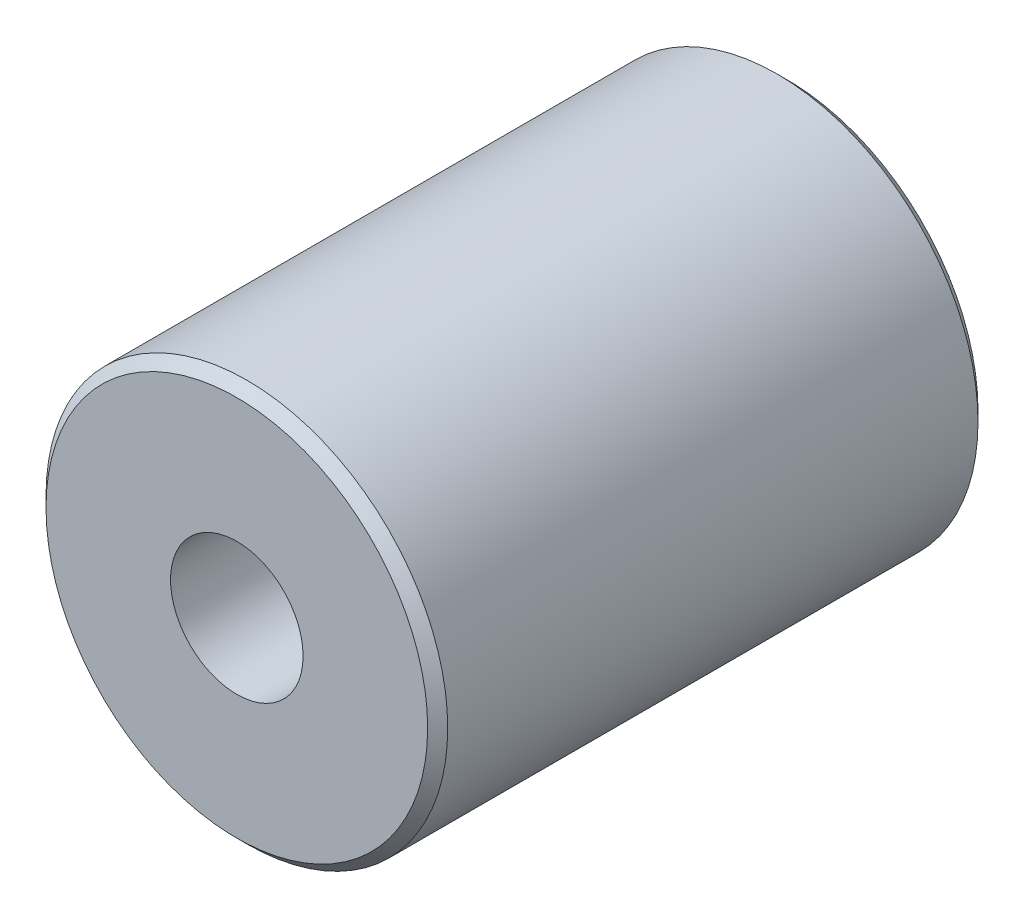
SolidWorks part; units mm, degrees
ref_plane "Front Plane" through (0, 0, 0) normal (0, 0, 1) x (1, 0, 0)
ref_plane "Top Plane" through (0, 0, 0) normal (0, 1, 0) x (1, 0, 0)
ref_plane "Right Plane" through (0, 0, 0) normal (1, 0, 0) x (0, 0, -1)
sketch "Sketch1" plane through (0, 0, 0) normal (0, 0, 1) x (1, 0, 0)
  circle A1 centre (0, 0) radius 5
extrude "Extrude1" add sketch "Sketch1" against normal blind 13.7
hole_wizard "M4x0.7 Tapped Hole1" positions "Sketch3" profile "Sketch2" tap size "M4x0.7" standard "Ansi Metric"
sketch "Sketch3" plane through (0, 0, 0) normal (0, 0, 1) x (1, 0, 0)
  point P0 (0, 0)
sketch "Sketch2" plane through (0, 0, 0) normal (1, 0, 0) x (0, -1, 0)
  line L0 (0, 0) -> (0, 10.9914)
  line L1 (0, 10.9914) -> (1.65, 10)
  line L2 (1.65, 10) -> (1.65, 0)
  line L5 (1.65, 0) -> (0, 0)
  line L10 (0, 10.9914) -> (-1.65, 10) construction
  line L11 (0, -6.35) -> (0, 107.95) construction
  dimension "Tap Drill Dia." = 3.3
  dimension "Tap Drill Depth" = 10
  dimension "Drill Angle" = 118
cosmetic thread "Hole Thread1"
hole_wizard "M4x0.7 Tapped Hole2" positions "Sketch5" profile "Sketch4" tap size "M4x0.7" standard "Ansi Metric"
sketch "Sketch5" plane through (0, 0, -13.7) normal (0, 0, -1) x (-1, 0, 0)
  point P0 (0, 0)
sketch "Sketch4" plane through (0, 0, -13.7) normal (1, 0, 0) x (0, 1, 0)
  line L0 (0, 0) -> (0, 10.9914)
  line L1 (0, 10.9914) -> (1.65, 10)
  line L2 (1.65, 10) -> (1.65, 0)
  line L5 (1.65, 0) -> (0, 0)
  line L10 (0, 10.9914) -> (-1.65, 10) construction
  line L11 (0, -6.35) -> (0, 107.95) construction
  dimension "Tap Drill Dia." = 3.3
  dimension "Tap Drill Depth" = 10
  dimension "Drill Angle" = 118
chamfer "Chamfer1" distance 0.25 angle 45 2 edges at (5, 0, -13.7) (5, 0, 0)
